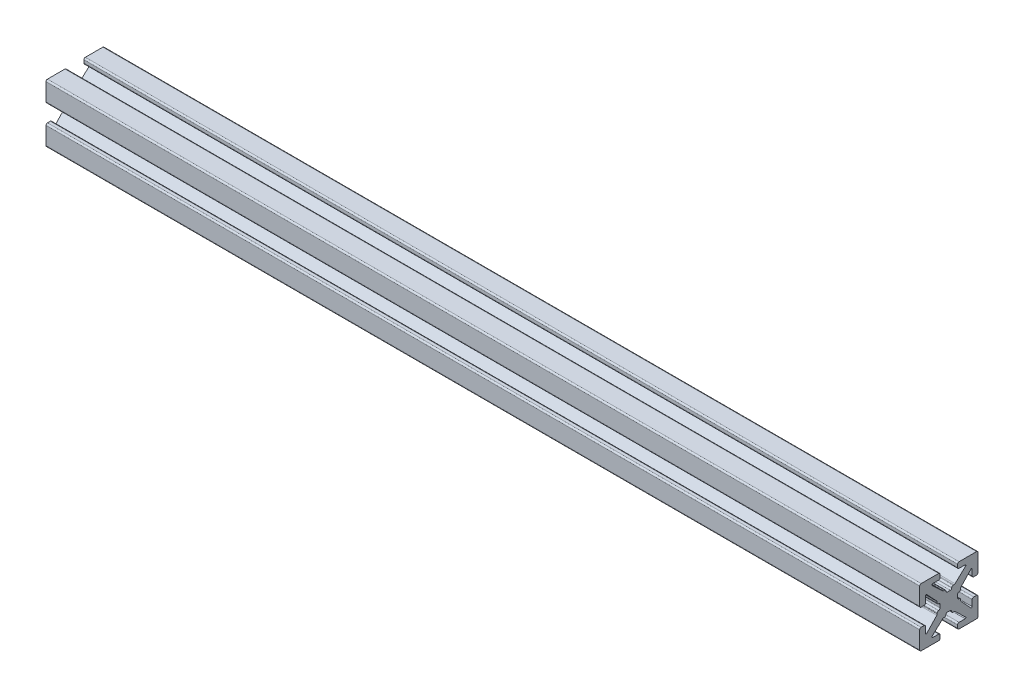
SolidWorks part; units mm, degrees
ref_plane "Front Plane" through (0, 0, 0) normal (0, 0, 1) x (1, 0, 0)
ref_plane "Top Plane" through (0, 0, 0) normal (0, 1, 0) x (1, 0, 0)
ref_plane "Right Plane" through (0, 0, 0) normal (1, 0, 0) x (0, 0, -1)
sketch "Sketch1" plane through (0, 0, 0) normal (1, 0, 0) x (0, 0, -1)
  line L0 (0, 0) -> (0, 1.4986) construction
  line L1 (-0.2413, 1.4986) -> (0.2413, 1.4986)
  line L2 (5.0038, 1.7526) -> (5.0038, 4.7498)
  line L3 (0.7493, 2.0066) -> (0.8899, 2.0066)
  line L4 (1.0639, 2.0756) -> (2.8908, 3.7937)
  line L5 (2.8038, 4.0132) -> (1.7526, 4.0132)
  line L6 (1.4986, 4.2672) -> (1.4986, 4.7498)
  line L7 (1.7526, 5.0038) -> (4.7498, 5.0038)
  line L8 (5.0038, 5.0038) -> (0, 0) construction
  line L9 (0, 0) -> (8.6271, 0) construction
  line L10 (0, 0) -> (0, 5.0038) construction
  line L11 (4.2672, 1.4986) -> (4.7498, 1.4986)
  line L12 (4.0132, 2.8038) -> (4.0132, 1.7526)
  line L13 (2.0756, 1.0639) -> (3.7937, 2.8908)
  line L14 (2.0066, 0.7493) -> (2.0066, 0.8899)
  line L15 (1.4986, -0.2413) -> (1.4986, 0.2413)
  line L16 (0, 0) -> (1.4986, 0) construction
  line L17 (-0.2413, -1.4986) -> (0.2413, -1.4986)
  line L18 (0.7493, -2.0066) -> (0.8899, -2.0066)
  line L19 (1.0639, -2.0756) -> (2.8908, -3.7937)
  line L20 (2.8038, -4.0132) -> (1.7526, -4.0132)
  line L21 (1.4986, -4.2672) -> (1.4986, -4.7498)
  line L22 (1.7526, -5.0038) -> (4.7498, -5.0038)
  line L23 (5.0038, -1.7526) -> (5.0038, -4.7498)
  line L24 (4.2672, -1.4986) -> (4.7498, -1.4986)
  line L25 (4.0132, -2.8038) -> (4.0132, -1.7526)
  line L26 (2.0756, -1.0639) -> (3.7937, -2.8908)
  line L27 (2.0066, -0.7493) -> (2.0066, -0.8899)
  line L28 (-0.7493, 2.0066) -> (-0.8899, 2.0066)
  line L29 (-1.0639, 2.0756) -> (-2.8908, 3.7937)
  line L30 (-2.8038, 4.0132) -> (-1.7526, 4.0132)
  line L31 (-1.4986, 4.2672) -> (-1.4986, 4.7498)
  line L32 (-1.7526, 5.0038) -> (-4.7498, 5.0038)
  line L33 (-5.0038, 1.7526) -> (-5.0038, 4.7498)
  line L34 (-4.2672, 1.4986) -> (-4.7498, 1.4986)
  line L35 (-4.0132, 2.8038) -> (-4.0132, 1.7526)
  line L36 (-2.0756, 1.0639) -> (-3.7937, 2.8908)
  line L37 (-2.0066, 0.7493) -> (-2.0066, 0.8899)
  line L38 (-1.4986, -0.2413) -> (-1.4986, 0.2413)
  line L39 (-2.0066, -0.7493) -> (-2.0066, -0.8899)
  line L40 (-2.0756, -1.0639) -> (-3.7937, -2.8908)
  line L41 (-4.0132, -2.8038) -> (-4.0132, -1.7526)
  line L42 (-4.2672, -1.4986) -> (-4.7498, -1.4986)
  line L43 (-5.0038, -1.7526) -> (-5.0038, -4.7498)
  line L44 (-1.7526, -5.0038) -> (-4.7498, -5.0038)
  line L45 (-1.4986, -4.2672) -> (-1.4986, -4.7498)
  line L46 (-2.8038, -4.0132) -> (-1.7526, -4.0132)
  line L47 (-1.0639, -2.0756) -> (-2.8908, -3.7937)
  line L48 (-0.7493, -2.0066) -> (-0.8899, -2.0066)
  arc A0 (2.8908, 3.7937) -> (2.8038, 4.0132) centre (2.8038, 3.8862) ccw
  arc A1 (0.4953, 1.7526) -> (0.7493, 2.0066) centre (0.7493, 1.7526) cw
  arc A2 (0.8899, 2.0066) -> (1.0639, 2.0756) centre (0.8899, 2.2606) ccw
  arc A3 (1.7526, 4.0132) -> (1.4986, 4.2672) centre (1.7526, 4.2672) cw
  arc A4 (1.4986, 4.7498) -> (1.7526, 5.0038) centre (1.7526, 4.7498) cw
  arc A5 (0.2413, 1.4986) -> (0.4953, 1.7526) centre (0.2413, 1.7526) ccw
  arc A6 (4.7498, 1.4986) -> (5.0038, 1.7526) centre (4.7498, 1.7526) ccw
  arc A7 (4.0132, 1.7526) -> (4.2672, 1.4986) centre (4.2672, 1.7526) ccw
  arc A8 (3.7937, 2.8908) -> (4.0132, 2.8038) centre (3.8862, 2.8038) cw
  arc A9 (2.0066, 0.8899) -> (2.0756, 1.0639) centre (2.2606, 0.8899) cw
  arc A10 (1.7526, 0.4953) -> (2.0066, 0.7493) centre (1.7526, 0.7493) ccw
  arc A11 (1.4986, 0.2413) -> (1.7526, 0.4953) centre (1.7526, 0.2413) cw
  arc A12 (0.2413, -1.4986) -> (0.4953, -1.7526) centre (0.2413, -1.7526) cw
  arc A13 (0.4953, -1.7526) -> (0.7493, -2.0066) centre (0.7493, -1.7526) ccw
  arc A14 (0.8899, -2.0066) -> (1.0639, -2.0756) centre (0.8899, -2.2606) cw
  arc A15 (2.8908, -3.7937) -> (2.8038, -4.0132) centre (2.8038, -3.8862) cw
  arc A16 (1.7526, -4.0132) -> (1.4986, -4.2672) centre (1.7526, -4.2672) ccw
  arc A17 (1.4986, -4.7498) -> (1.7526, -5.0038) centre (1.7526, -4.7498) ccw
  arc A18 (4.7498, -1.4986) -> (5.0038, -1.7526) centre (4.7498, -1.7526) cw
  arc A19 (4.0132, -1.7526) -> (4.2672, -1.4986) centre (4.2672, -1.7526) cw
  arc A20 (3.7937, -2.8908) -> (4.0132, -2.8038) centre (3.8862, -2.8038) ccw
  arc A21 (2.0066, -0.8899) -> (2.0756, -1.0639) centre (2.2606, -0.8899) ccw
  arc A22 (1.7526, -0.4953) -> (2.0066, -0.7493) centre (1.7526, -0.7493) cw
  arc A23 (1.4986, -0.2413) -> (1.7526, -0.4953) centre (1.7526, -0.2413) ccw
  arc A24 (-0.2413, 1.4986) -> (-0.4953, 1.7526) centre (-0.2413, 1.7526) cw
  arc A25 (-0.4953, 1.7526) -> (-0.7493, 2.0066) centre (-0.7493, 1.7526) ccw
  arc A26 (-0.8899, 2.0066) -> (-1.0639, 2.0756) centre (-0.8899, 2.2606) cw
  arc A27 (-2.8908, 3.7937) -> (-2.8038, 4.0132) centre (-2.8038, 3.8862) cw
  arc A28 (-1.7526, 4.0132) -> (-1.4986, 4.2672) centre (-1.7526, 4.2672) ccw
  arc A29 (-1.4986, 4.7498) -> (-1.7526, 5.0038) centre (-1.7526, 4.7498) ccw
  arc A30 (-4.7498, 1.4986) -> (-5.0038, 1.7526) centre (-4.7498, 1.7526) cw
  arc A31 (-4.0132, 1.7526) -> (-4.2672, 1.4986) centre (-4.2672, 1.7526) cw
  arc A32 (-3.7937, 2.8908) -> (-4.0132, 2.8038) centre (-3.8862, 2.8038) ccw
  arc A33 (-2.0066, 0.8899) -> (-2.0756, 1.0639) centre (-2.2606, 0.8899) ccw
  arc A34 (-1.7526, 0.4953) -> (-2.0066, 0.7493) centre (-1.7526, 0.7493) cw
  arc A35 (-1.4986, 0.2413) -> (-1.7526, 0.4953) centre (-1.7526, 0.2413) ccw
  arc A36 (-1.4986, -0.2413) -> (-1.7526, -0.4953) centre (-1.7526, -0.2413) cw
  arc A37 (-1.7526, -0.4953) -> (-2.0066, -0.7493) centre (-1.7526, -0.7493) ccw
  arc A38 (-2.0066, -0.8899) -> (-2.0756, -1.0639) centre (-2.2606, -0.8899) cw
  arc A39 (-3.7937, -2.8908) -> (-4.0132, -2.8038) centre (-3.8862, -2.8038) cw
  arc A40 (-4.0132, -1.7526) -> (-4.2672, -1.4986) centre (-4.2672, -1.7526) ccw
  arc A41 (-4.7498, -1.4986) -> (-5.0038, -1.7526) centre (-4.7498, -1.7526) ccw
  arc A42 (-1.4986, -4.7498) -> (-1.7526, -5.0038) centre (-1.7526, -4.7498) cw
  arc A43 (-1.7526, -4.0132) -> (-1.4986, -4.2672) centre (-1.7526, -4.2672) cw
  arc A44 (-2.8908, -3.7937) -> (-2.8038, -4.0132) centre (-2.8038, -3.8862) ccw
  arc A45 (-0.8899, -2.0066) -> (-1.0639, -2.0756) centre (-0.8899, -2.2606) ccw
  arc A46 (-0.4953, -1.7526) -> (-0.7493, -2.0066) centre (-0.7493, -1.7526) cw
  arc A47 (-0.2413, -1.4986) -> (-0.4953, -1.7526) centre (-0.2413, -1.7526) ccw
  arc A48 (-4.7498, 5.0038) -> (-5.0038, 4.7498) centre (-4.7498, 4.7498) ccw
  arc A49 (-5.0038, -4.7498) -> (-4.7498, -5.0038) centre (-4.7498, -4.7498) ccw
  arc A50 (4.7498, -5.0038) -> (5.0038, -4.7498) centre (4.7498, -4.7498) ccw
  arc A51 (4.7498, 5.0038) -> (5.0038, 4.7498) centre (4.7498, 4.7498) cw
  point P14 (3.1242, 4.0132)
  point P19 (0.9906, 2.0066)
  point P150 (0, -1.4986)
  point P152 (-5.0038, 5.0038)
  point P155 (-5.0038, -5.0038)
  point P158 (5.0038, -5.0038)
  dimension "D10" = 0.127
  dimension "D11" = 0.254
  dimension "D2" = 0.254
  dimension "D1" = 10.0076
  dimension "D3" = 2.9972
  dimension "D4" = 0.508
  dimension "D5" = 2.9972
  dimension "D6" = 0.9906
  dimension "D7" = 1.6256
  dimension "D8" = 1.9812
  dimension "D9" = 0.9906
extrude "Boss.-Extru.1" add sketch "Sketch1" along normal blind 150
